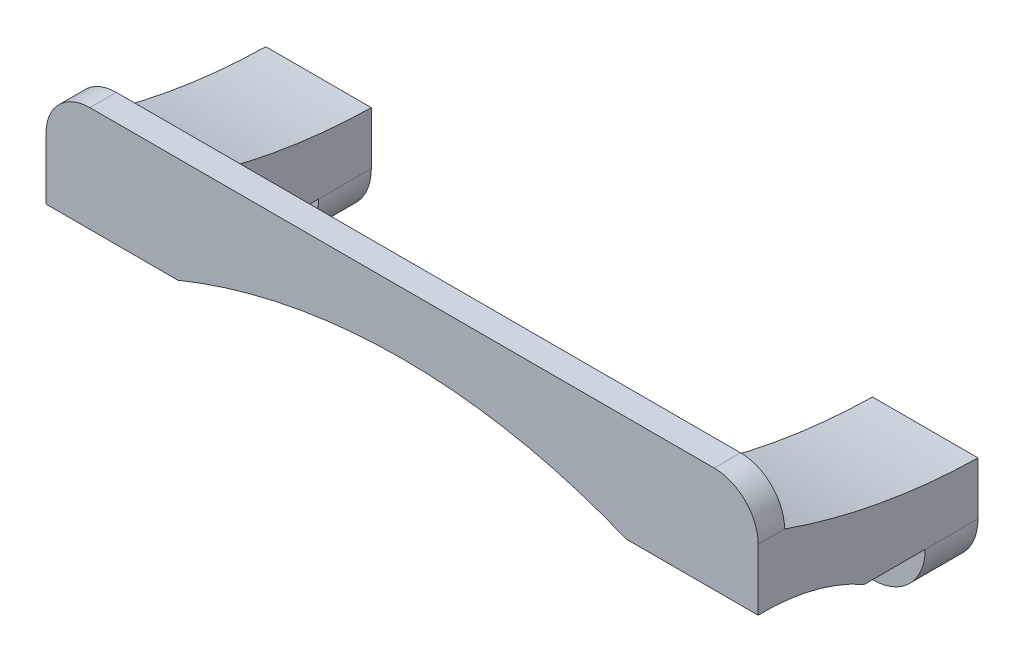
SolidWorks part; units mm, degrees
ref_plane "Ön Düzlem" through (0, 0, 0) normal (0, 0, 1) x (1, 0, 0)
ref_plane "Üst Düzlem" through (0, 0, 0) normal (0, 1, 0) x (1, 0, 0)
ref_plane "Sağ Düzlem" through (0, 0, 0) normal (1, 0, 0) x (0, 0, -1)
sketch "Çizim1" plane through (0, 0, 0) normal (0, 0, 1) x (1, 0, 0)
  circle A0 centre (34.5, 0) radius 6
  circle A1 centre (34.5, 0) radius 1.7
  circle A2 centre (-34.5, 0) radius 1.7
  circle A3 centre (-34.5, 0) radius 6
extrude "Yükseklik-Ekstrüzyon1" add sketch "Çizim1" along normal blind 22
sketch "Çizim2" plane through (0, 0, 22) normal (0, 0, 1) x (1, 0, 0)
  line L0 (-40.5, 0) -> (-40.5, 10)
  line L2 (40.5, 10) -> (40.5, 0)
  line L3 (-40.5, 10) -> (-40.5, 15)
  line L4 (-40.5, 15) -> (40.5, 15)
  line L5 (40.5, 15) -> (40.5, 10)
  circle A0 centre (-34.5, 0) radius 6 construction
  circle A1 centre (34.5, 0) radius 6 construction
  arc A2 (-40.5, 0) -> (-31.3052, -5.0787) centre (-34.5, 0) ccw
  arc A3 (31.3052, -5.0787) -> (40.5, 0) centre (34.5, 0) ccw
  arc A4 (-16.018, -0.2872) -> (-31.3052, -5.0787) centre (-7.011, -55.8065) ccw
  arc A5 (16.018, -0.2872) -> (31.3052, -5.0787) centre (7.011, -55.8065) cw
  circle A6 centre (-34.5, 0) radius 1.7
  arc A7 (-16.018, -0.2872) -> (0, 6) centre (1.212, -20.6361) cw
  arc A8 (16.018, -0.2872) -> (0, 6) centre (-1.212, -20.6361) ccw
  circle A9 centre (34.5, 0) radius 1.7
extrude "Yükseklik-Ekstrüzyon2" add sketch "Çizim2" along normal blind 3
fillet "Radyus2" radius 5 2 edges at (-40.5, 15, 23.5) (40.5, 15, 23.5)
sketch "Çizim4" plane through (0, 0, 25) normal (0, 0, 1) x (1, 0, 0)
  circle A0 centre (-35, 5) radius 1.6
  circle A1 centre (35, 5) radius 1.6
extrude "Kes-Ekstrüzyon1" cut sketch "Çizim4" against normal blind 10
sketch "Çizim5" plane through (-40.5, 0, 0) normal (-1, 0, 0) x (0, 0, 1)
  line L0 (0, 6) -> (0, 0)
  line L1 (0, 0) -> (22, 0)
  line L2 (22, 0) -> (22, 10)
  arc A0 (22, 10) -> (0, 6) centre (-1.3472, 75.9094) cw
extrude "Yükseklik-Ekstrüzyon5" add sketch "Çizim5" against normal blind 12
sketch "Çizim6" plane through (40.5, 0, 0) normal (1, 0, 0) x (0, 0, -1)
  line L2 (-22, 0) -> (-22, 10)
  line L3 (0, 0) -> (-22, 0)
  line L4 (0, 6) -> (0, 0)
  arc A1 (-22, 10) -> (0, 6) centre (1.3472, 75.9094) ccw
extrude "Yükseklik-Ekstrüzyon6" add sketch "Çizim6" against normal blind 12
sketch "Çizim9" plane through (-40.5, 0, 0) normal (-1, 0, 0) x (0, 0, 1)
  line L0 (25, 3) -> (25, -6.8896)
  line L1 (25, -6.8896) -> (6, -6)
  arc A2 (6, -6) -> (25, 3) centre (24.3455, -20.1739) cw
extrude "Kes-Ekstrüzyon2" cut sketch "Çizim9" against normal blind 97
sketch "Çizim10" plane through (-40.5, 0, 0) normal (-1, 0, 0) x (0, 0, 1)
  line L1 (12.9231, 0) -> (6, 0)
  line L2 (12.9231, 0) -> (12.9231, -6.6175)
  line L3 (12.9231, -6.6175) -> (6, -6.6175)
  line L4 (6, 0) -> (6, -6.6175)
extrude "Kes-Ekstrüzyon3" cut sketch "Çizim10" against normal blind 97
sketch "Çizim11" plane through (0, 0, 6) normal (0, 0, 1) x (1, 0, 0)
  line L0 (-40.5, 0) -> (-28.5, 0) construction
  circle A0 centre (-34.5, 0) radius 3
  circle A1 centre (34.5, 0) radius 3
extrude "Kes-Ekstrüzyon4" cut sketch "Çizim11" along normal blind 97
sketch "Çizim12" plane through (0, 0, 25) normal (0, 0, 1) x (1, 0, 0)
  circle A0 centre (-35, 5) radius 1.6
  circle A1 centre (35, 5) radius 1.6
extrude "Yükseklik-Ekstrüzyon8" add sketch "Çizim12" against normal blind 10
sketch "Çizim13" plane through (0, 0, 0) normal (0, 0, -1) x (-1, 0, 0)
  line L0 (32.8, 0) -> (36.2, 0) construction
  line L1 (-32.8, 0) -> (-36.2, 0) construction
  circle A0 centre (34.5, 0) radius 1.7
  circle A1 centre (-34.5, 0) radius 1.7
extrude "Kes-Ekstrüzyon5" cut sketch "Çizim13" against normal blind 10
sketch "Çizim15" plane through (0, 0, 25) normal (0, 0, 1) x (1, 0, 0)
  line L0 (-25.5, 3) -> (-25.5, -6.329)
  line L2 (-25.5, -6.329) -> (21.9824, -11.6826)
  line L3 (21.9824, -11.6826) -> (25.5, 3)
  arc A2 (-25.5, 3) -> (25.5, 3) centre (0, -59.1409) cw
extrude "Kes-Ekstrüzyon6" cut sketch "Çizim15" against normal blind 10
